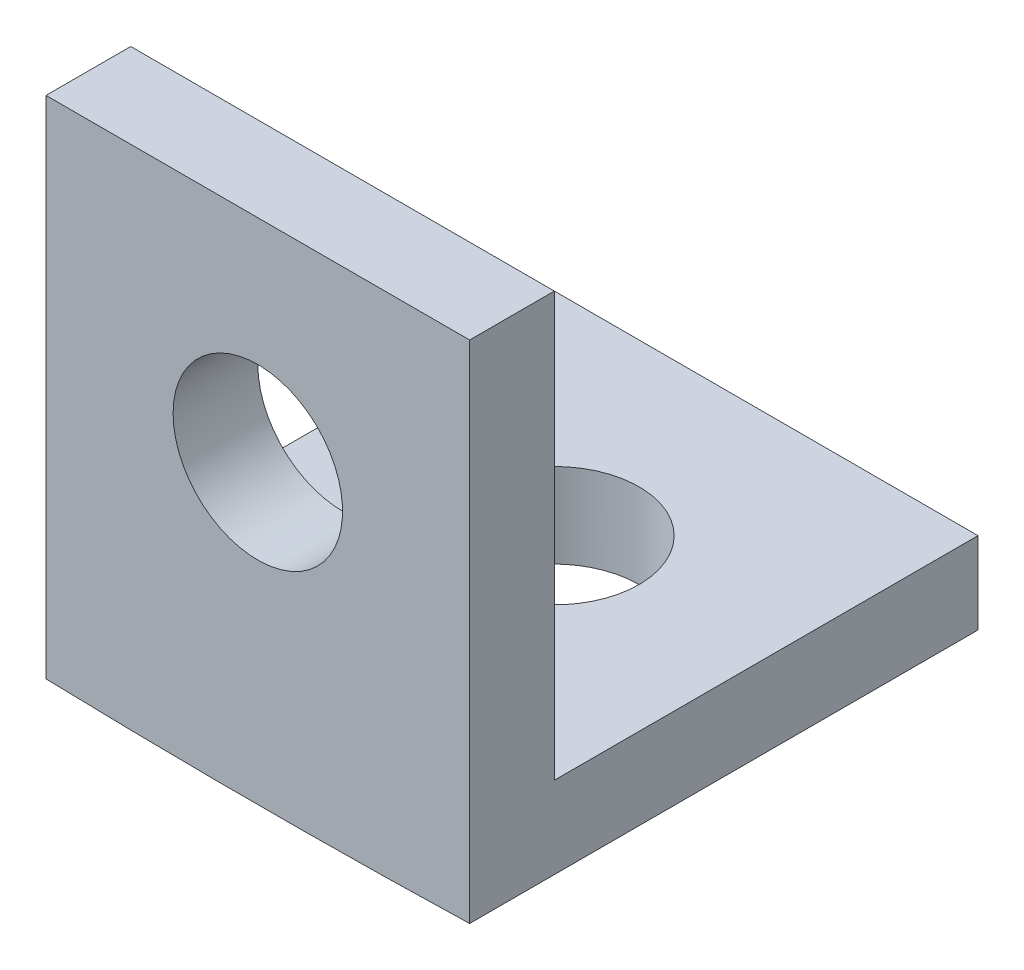
SolidWorks part; units mm, degrees
ref_plane "Plano frontal" through (0, 0, 0) normal (0, 0, 1) x (1, 0, 0)
ref_plane "Plano superior" through (0, 0, 0) normal (0, 1, 0) x (1, 0, 0)
ref_plane "Plano direito" through (0, 0, 0) normal (1, 0, 0) x (0, 0, -1)
sketch "Esboço1" plane through (0, 0, 0) normal (0, 0, 1) x (1, 0, 0)
  line L1 (2.5, 3) -> (-2.5, 3)
  line L2 (2.5, 3) -> (2.5, -3)
  line L3 (2.5, -3) -> (-2.5, -3)
  line L4 (-2.5, 3) -> (-2.5, -3)
  line L5 (2.5, 3) -> (-2.5, -3) construction
  line L6 (2.5, -3) -> (-2.5, 3) construction
  point P0 (0, 0)
  dimension "D1" = 5
  dimension "D2" = 6
extrude "Ressalto-extrusão1" add sketch "Esboço1" against normal blind 1
sketch "Esboço2" plane through (0, 0, -1) normal (0, 0, -1) x (-1, 0, 0)
  line L0 (-2.5, -2) -> (2.5, -2)
  line L1 (-2.5, -3) -> (-2.5, 3) construction
  line L2 (2.5, 3) -> (2.5, -3) construction
  line L3 (2.5, -2) -> (2.5, -3)
  line L4 (2.5, -3) -> (-2.5, -3)
  line L5 (-2.5, -3) -> (-2.5, -2)
  dimension "D1" = 1
extrude "Ressalto-extrusão2" add sketch "Esboço2" along normal blind 5
sketch "Esboço3" plane through (0, 0, 0) normal (0, 0, 1) x (1, 0, 0)
  line L0 (-2.5, -3) -> (2.5, -3) construction
  line L1 (0, 85) -> (0, 0) construction
  circle A0 centre (0, 85) radius 88
  line M2 (-2.5, 3) -> (-2.5, -3)
  line M3 (-2.5, -3) -> (2.5, -3)
  line M4 (2.5, -3) -> (2.5, 3)
  dimension "D1" = 176
extrude "Corte-extrusão1" cut sketch "Esboço3" against normal up to next contours A0 M2 M3 | A0 M3 M4
sketch "Esboço4" plane through (0, -2, 0) normal (0, 1, 0) x (1, 0, 0)
  line L0 (0, 6) -> (0, 3.5) construction
  line L1 (-2.5, 6) -> (2.5, 6) construction
  line L2 (0, 3.5) -> (-2.5, 3.5) construction
  line L3 (-2.5, 6) -> (-2.5, 1) construction
  circle A0 centre (0, 3.5) radius 1
  dimension "D1" = 2
extrude "Corte-extrusão2" cut sketch "Esboço4" against normal up to next
sketch "Esboço5" plane through (0, 0, -1) normal (0, 0, -1) x (-1, 0, 0)
  line L0 (0, 0.5) -> (0, 3) construction
  line L1 (-2.5, 3) -> (2.5, 3) construction
  line L2 (0, 0.5) -> (-2.5, 0.5) construction
  line L3 (-2.5, -2) -> (-2.5, 3) construction
  circle A0 centre (0, 0.5) radius 1
  dimension "D1" = 2
extrude "Corte-extrusão3" cut sketch "Esboço5" against normal up to next
